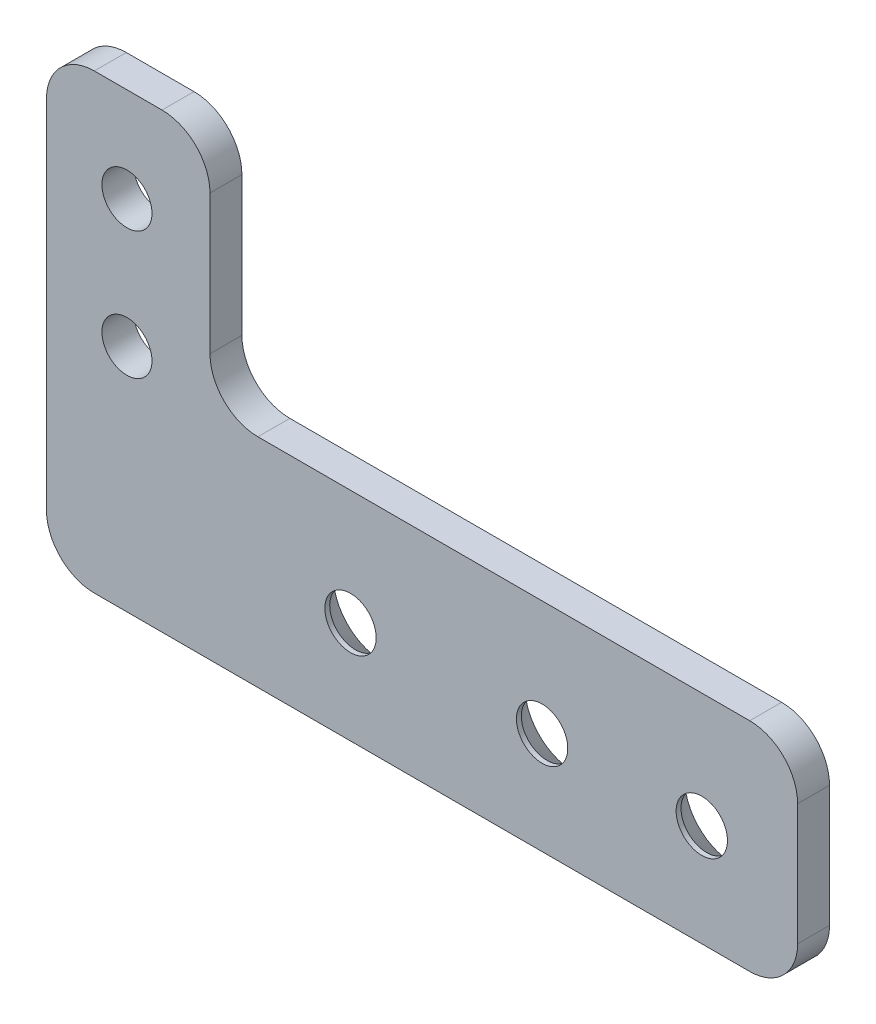
SolidWorks part; units mm, degrees
material "6061-T6 (SS)"
ref_plane "Front Plane" through (0, 0, 0) normal (0, 0, 1) x (1, 0, 0)
ref_plane "Top Plane" through (0, 0, 0) normal (0, 1, 0) x (1, 0, 0)
ref_plane "Right Plane" through (0, 0, 0) normal (1, 0, 0) x (0, 0, -1)
sketch "Sketch1" plane through (0, 0, 0) normal (0, 0, 1) x (1, 0, 0)
  line L0 (41.275, -11.049) -> (-33.401, -11.049) construction
  line L1 (-41.275, -23.749) -> (41.275, -23.749)
  line L2 (-41.275, -23.749) -> (-41.275, 23.749)
  line L3 (-41.275, 23.749) -> (41.275, 23.749)
  line L4 (41.275, -23.749) -> (41.275, 23.749)
  line L5 (-41.275, -23.749) -> (41.275, 23.749) construction
  line L6 (-41.275, 23.749) -> (41.275, -23.749) construction
  line L7 (41.275, 23.749) -> (-17.145, 23.749)
  line L8 (41.275, 23.749) -> (41.275, 0.381)
  line L9 (41.275, 0.381) -> (-17.145, 0.381)
  line L10 (-17.145, 23.749) -> (-17.145, 0.381)
  line L11 (-41.275, -23.749) -> (-33.401, -23.749)
  line L12 (-41.275, -23.749) -> (-41.275, 23.749)
  line L13 (-41.275, 23.749) -> (-33.401, 23.749)
  line L14 (-33.401, -23.749) -> (-33.401, 23.749)
  line L15 (-33.401, -23.749) -> (41.275, -23.749)
  line L16 (-33.401, -23.749) -> (-33.401, -21.209)
  line L17 (-33.401, -21.209) -> (41.275, -21.209)
  line L18 (41.275, -23.749) -> (41.275, -21.209)
  line L19 (-33.401, 23.876) -> (-17.145, 23.876) construction
  circle A0 centre (-25.4, -11.049) radius 2.4892
  circle A1 centre (-25.4, 1.651) radius 2.4892
  circle A2 centre (-25.4, 14.351) radius 2.4892
  point P0 (0, 0)
  point P22 (31.75, -11.049)
  point P23 (-3.175, -11.049)
  point P24 (15.875, -11.049)
  dimension "D7" = 4.9784
  dimension "D1" = 82.55
  dimension "D2" = 47.498
  dimension "D3" = 24.13
  dimension "D4" = 24.13
  dimension "D5" = 7.874
  dimension "D6" = 47.498
  dimension "D8" = 22.225
  dimension "D9" = 12.7
  dimension "D10" = 12.7
  dimension "D11" = 12.7
  dimension "D12" = 9.525
  dimension "D13" = 57.15
  dimension "D14" = 15.875
  dimension "D15" = 15.875
  dimension "D16" = 2.54
extrude "Boss-Extrude1" add sketch "Sketch1" along normal blind 3.175
fillet "Fillet1" radius 4.7625 6 edges at (-33.401, 23.749, 1.5875) (-17.145, 23.749, 1.5875) (-17.145, 0.381, 1.5875) (41.275, 0.381, 1.5875) (41.275, -21.209, 1.5875) (-33.401, -21.209, 1.5875)
hole_wizard "CSK for #10 Flat Head Machine Screw3" positions "Sketch6" profile "Sketch7" countersink size "#10" standard "ANSI Inch" end condition through all
sketch "Sketch6" plane through (0, 0, 0) normal (0, 0, -1) x (-1, 0, 0)
  point P0 (-31.75, -11.049)
  point P3 (-15.875, -11.049)
  point P6 (3.175, -11.049)
sketch "Sketch7" plane through (31.75, -11.049, 0) normal (1, 0, 0) x (0, 1, 0)
  line L0 (0, 0) -> (0, 3.175)
  line L1 (0, 3.175) -> (2.5527, 3.175)
  line L2 (2.5527, 3.175) -> (2.5527, 2.6882)
  line L3 (2.5527, 2.6882) -> (4.8895, 0)
  line L5 (4.8895, 0) -> (0, 0)
  line L6 (-2.5527, 2.6882) -> (-4.8895, 0) construction
  line L11 (0, -6.35) -> (0, 107.95) construction
  dimension "Thru Hole Dia." = 5.1054
  dimension "Thru Hole Depth" = 3.175
  dimension "Near C'Sink Dia." = 9.779
  dimension "Near C'Sink Angle" = 82
